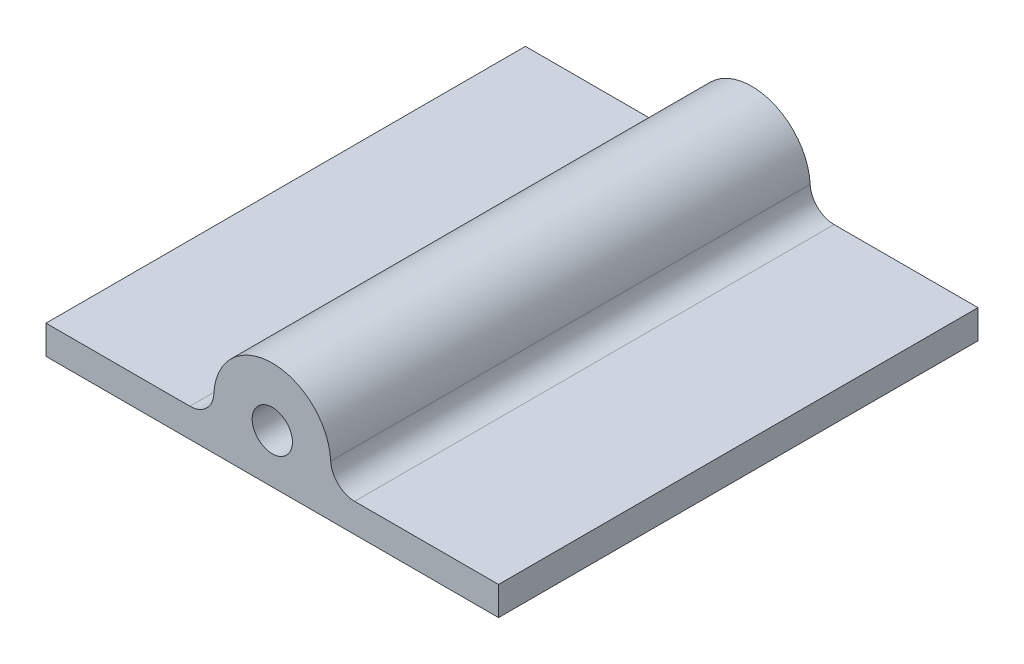
SolidWorks part; units mm, degrees
ref_plane "Front Plane" through (0, 0, 0) normal (0, 0, 1) x (1, 0, 0)
ref_plane "Top Plane" through (0, 0, 0) normal (0, 1, 0) x (1, 0, 0)
ref_plane "Right Plane" through (0, 0, 0) normal (1, 0, 0) x (0, 0, -1)
sketch "Sketch2" plane through (0, 0, 0) normal (0, 0, 1) x (1, 0, 0)
  line L1 (15.4406, -4.8815) -> (15.4406, -0.6815)
  line L2 (-8.9594, -4.8815) -> (-8.9594, -0.6815)
  line L3 (-8.9594, -4.8815) -> (-43.9594, -4.8815)
  line L4 (-43.9594, -4.8815) -> (-43.9594, -10.8815)
  line L5 (-43.9594, -10.8815) -> (50.4406, -10.8815)
  line L6 (50.4406, -10.8815) -> (50.4406, -4.8815)
  line L7 (50.4406, -4.8815) -> (15.4406, -4.8815)
  line L8 (-8.9594, -4.8815) -> (15.4406, -4.8815) construction
  arc A0 (-8.9594, -0.6815) -> (15.4406, -0.6815) centre (3.2406, -0.6815) cw
  circle A1 centre (3.2406, -0.6815) radius 4.2
  point P9 (9.7301, 0)
  point P11 (11.7453, -0.0338)
  point P12 (0, 0)
  point P13 (0, 0)
  point P14 (41.7569, -2.4088)
  point P15 (37.0788, -4.7838)
  point P16 (0, 0)
  point P17 (11.6733, -0.6815)
  dimension "D1" = 8.4
  dimension "D2" = 8
  dimension "D3" = 6
  dimension "D4" = 35
extrude "Boss-Extrude1" add sketch "Sketch2" along normal blind 100
fillet "Fillet1" radius 5 2 edges at (-8.9594, -4.8815, 50) (15.4406, -4.8815, 50)
